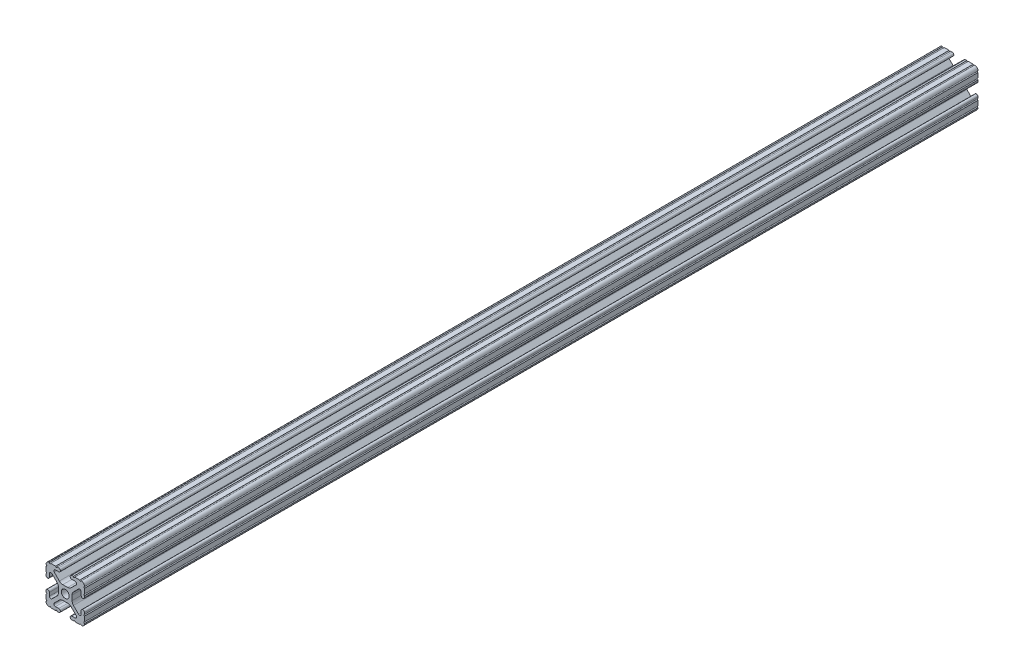
SolidWorks part; units mm, degrees
ref_plane "Front Plane" through (0, 0, 0) normal (0, 0, 1) x (1, 0, 0)
ref_plane "Top Plane" through (0, 0, 0) normal (0, 1, 0) x (1, 0, 0)
ref_plane "Right Plane" through (0, 0, 0) normal (1, 0, 0) x (0, 0, -1)
ref_plane "Plane1" through (0, 0, -450.85) normal (0, 0, -1) x (-1, 0, 0)
sketch "Sketch1" plane through (0, 0, -450.85) normal (0, 0, -1) x (-1, 0, 0)
  line L0 (12.7, -9.5504) -> (12.7, -6.3331)
  line L1 (12.7, -5.3171) -> (12.7, -4.3434)
  line L2 (10.4902, -4.3434) -> (10.4902, -6.4748)
  line L3 (8.7558, -7.1932) -> (5.4257, -3.8632)
  line L4 (4.4958, -1.6181) -> (4.4958, 1.6181)
  line L5 (5.4257, 3.8632) -> (8.7558, 7.1932)
  line L6 (10.4902, 6.4748) -> (10.4902, 4.3434)
  line L7 (12.7, 4.3434) -> (12.7, 5.3171)
  line L8 (12.7, 6.3331) -> (12.7, 9.5504)
  line L9 (9.5504, 12.7) -> (6.3331, 12.7)
  line L10 (5.3171, 12.7) -> (4.3434, 12.7)
  line L11 (4.3434, 10.4902) -> (6.4748, 10.4902)
  line L12 (7.1932, 8.7558) -> (3.8632, 5.4257)
  line L13 (1.6181, 4.4958) -> (-1.6181, 4.4958)
  line L14 (-3.8632, 5.4257) -> (-7.1932, 8.7558)
  line L15 (-6.4748, 10.4902) -> (-4.3434, 10.4902)
  line L16 (-4.3434, 12.7) -> (-5.3171, 12.7)
  line L17 (-6.3331, 12.7) -> (-9.5504, 12.7)
  line L18 (-12.7, 9.5504) -> (-12.7, 6.3331)
  line L19 (-12.7, 5.3171) -> (-12.7, 4.3434)
  line L20 (-10.4902, 4.3434) -> (-10.4902, 6.4748)
  line L21 (-8.7558, 7.1932) -> (-5.4257, 3.8632)
  line L22 (-4.4958, 1.6181) -> (-4.4958, -1.6181)
  line L23 (-5.4257, -3.8632) -> (-8.7558, -7.1932)
  line L24 (-10.4902, -6.4748) -> (-10.4902, -4.3434)
  line L25 (-12.7, -4.3434) -> (-12.7, -5.3171)
  line L26 (-12.7, -6.3331) -> (-12.7, -9.5504)
  line L27 (-9.5504, -12.7) -> (-6.3331, -12.7)
  line L28 (-5.3171, -12.7) -> (-4.3434, -12.7)
  line L29 (-4.3434, -10.4902) -> (-6.4748, -10.4902)
  line L30 (-7.1932, -8.7558) -> (-3.8632, -5.4257)
  line L31 (-1.6181, -4.4958) -> (1.6181, -4.4958)
  line L32 (3.8632, -5.4257) -> (7.1932, -8.7558)
  line L33 (6.4748, -10.4902) -> (4.3434, -10.4902)
  line L34 (4.3434, -12.7) -> (5.3171, -12.7)
  line L35 (6.3331, -12.7) -> (9.5504, -12.7)
  arc A0 (12.6998, -10.5664) -> (12.7, -9.5504) centre (12.7, -10.0584) cw
  arc A1 (12.7, -6.3331) -> (12.7, -5.3171) centre (12.7, -5.8251) cw
  arc A2 (12.7, -4.3434) -> (10.4902, -4.3434) centre (11.5951, -4.3434) ccw
  arc A3 (10.4902, -6.4748) -> (8.7558, -7.1932) centre (9.4742, -6.4748) cw
  arc A4 (5.4257, -3.8632) -> (4.4958, -1.6181) centre (7.6708, -1.6181) cw
  arc A5 (4.4958, 1.6181) -> (5.4257, 3.8632) centre (7.6708, 1.6181) cw
  arc A6 (8.7558, 7.1932) -> (10.4902, 6.4748) centre (9.4742, 6.4748) cw
  arc A7 (10.4902, 4.3434) -> (12.7, 4.3434) centre (11.5951, 4.3434) ccw
  arc A8 (12.7, 5.3171) -> (12.7, 6.3331) centre (12.7, 5.8251) cw
  arc A9 (12.7, 9.5504) -> (12.6998, 10.5664) centre (12.7, 10.0584) cw
  arc A10 (12.6998, 10.5664) -> (10.5664, 12.6998) centre (10.5918, 10.5918) ccw
  arc A11 (10.5664, 12.6998) -> (9.5504, 12.7) centre (10.0584, 12.7) cw
  arc A12 (6.3331, 12.7) -> (5.3171, 12.7) centre (5.8251, 12.7) cw
  arc A13 (4.3434, 12.7) -> (4.3434, 10.4902) centre (4.3434, 11.5951) ccw
  arc A14 (6.4748, 10.4902) -> (7.1932, 8.7558) centre (6.4748, 9.4742) cw
  arc A15 (3.8632, 5.4257) -> (1.6181, 4.4958) centre (1.6181, 7.6708) cw
  arc A16 (-1.6181, 4.4958) -> (-3.8632, 5.4257) centre (-1.6181, 7.6708) cw
  arc A17 (-7.1932, 8.7558) -> (-6.4748, 10.4902) centre (-6.4748, 9.4742) cw
  arc A18 (-4.3434, 10.4902) -> (-4.3434, 12.7) centre (-4.3434, 11.5951) ccw
  arc A19 (-5.3171, 12.7) -> (-6.3331, 12.7) centre (-5.8251, 12.7) cw
  arc A20 (-9.5504, 12.7) -> (-10.5664, 12.6998) centre (-10.0584, 12.7) cw
  arc A21 (-10.5664, 12.6998) -> (-12.6998, 10.5664) centre (-10.5918, 10.5918) ccw
  arc A22 (-12.6998, 10.5664) -> (-12.7, 9.5504) centre (-12.7, 10.0584) cw
  arc A23 (-12.7, 6.3331) -> (-12.7, 5.3171) centre (-12.7, 5.8251) cw
  arc A24 (-12.7, 4.3434) -> (-10.4902, 4.3434) centre (-11.5951, 4.3434) ccw
  arc A25 (-10.4902, 6.4748) -> (-8.7558, 7.1932) centre (-9.4742, 6.4748) cw
  arc A26 (-5.4257, 3.8632) -> (-4.4958, 1.6181) centre (-7.6708, 1.6181) cw
  arc A27 (-4.4958, -1.6181) -> (-5.4257, -3.8632) centre (-7.6708, -1.6181) cw
  arc A28 (-8.7558, -7.1932) -> (-10.4902, -6.4748) centre (-9.4742, -6.4748) cw
  arc A29 (-10.4902, -4.3434) -> (-12.7, -4.3434) centre (-11.5951, -4.3434) ccw
  arc A30 (-12.7, -5.3171) -> (-12.7, -6.3331) centre (-12.7, -5.8251) cw
  arc A31 (-12.7, -9.5504) -> (-12.6998, -10.5664) centre (-12.7, -10.0584) cw
  arc A32 (-12.6998, -10.5664) -> (-10.5664, -12.6998) centre (-10.5918, -10.5918) ccw
  arc A33 (-10.5664, -12.6998) -> (-9.5504, -12.7) centre (-10.0584, -12.7) cw
  arc A34 (-6.3331, -12.7) -> (-5.3171, -12.7) centre (-5.8251, -12.7) cw
  arc A35 (-4.3434, -12.7) -> (-4.3434, -10.4902) centre (-4.3434, -11.5951) ccw
  arc A36 (-6.4748, -10.4902) -> (-7.1932, -8.7558) centre (-6.4748, -9.4742) cw
  arc A37 (-3.8632, -5.4257) -> (-1.6181, -4.4958) centre (-1.6181, -7.6708) cw
  arc A38 (1.6181, -4.4958) -> (3.8632, -5.4257) centre (1.6181, -7.6708) cw
  arc A39 (7.1932, -8.7558) -> (6.4748, -10.4902) centre (6.4748, -9.4742) cw
  arc A40 (4.3434, -10.4902) -> (4.3434, -12.7) centre (4.3434, -11.5951) ccw
  arc A41 (5.3171, -12.7) -> (6.3331, -12.7) centre (5.8251, -12.7) cw
  arc A42 (9.5504, -12.7) -> (10.5664, -12.6998) centre (10.0584, -12.7) cw
  arc A43 (10.5664, -12.6998) -> (12.6998, -10.5664) centre (10.5918, -10.5918) ccw
  circle A44 centre (0, 0) radius 2.6035
extrude "Boss-Extrude1" add sketch "Sketch1" against normal blind 589.153
ref_plane "Plane2" through (0, 0, -156.2735) normal (0, 0, 1) x (1, 0, 0)
